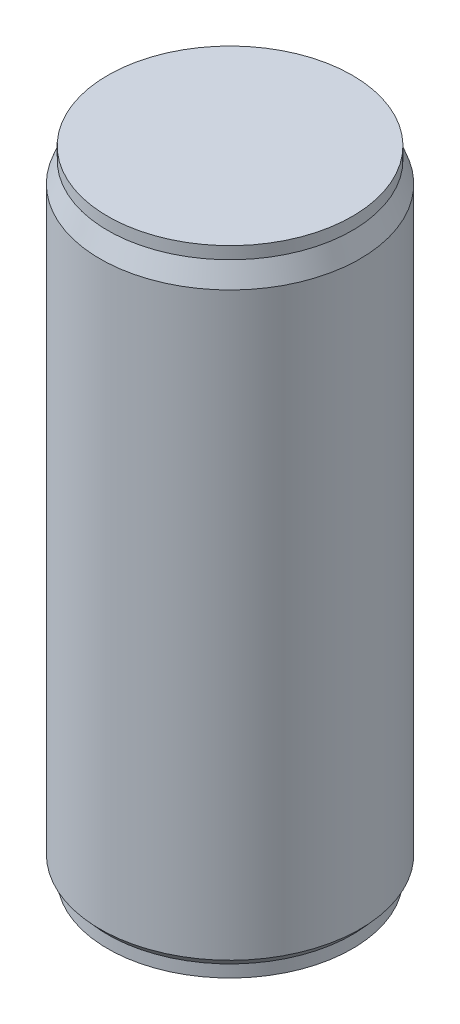
SolidWorks part; units mm, degrees
ref_plane "Front Plane" through (0, 0, 0) normal (0, 0, 1) x (1, 0, 0)
ref_plane "Top Plane" through (0, 0, 0) normal (0, 1, 0) x (1, 0, 0)
ref_plane "Right Plane" through (0, 0, 0) normal (1, 0, 0) x (0, 0, -1)
sketch "Sketch1" plane through (0, 0, 0) normal (0, 0, 1) x (1, 0, 0)
  line L0 (0, 0) -> (0, 131.7625)
  line L1 (0, 131.7625) -> (25.4, 131.7625)
  line L2 (25.4, 131.7625) -> (25.4, 129.2225)
  line L3 (25.4, 129.2225) -> (26.9875, 124.9045)
  line L4 (26.9875, 124.9045) -> (26.9875, 4.318)
  line L5 (26.9875, 4.318) -> (25.4, 2.54)
  line L6 (25.4, 2.54) -> (25.4, 0)
  line L7 (25.4, 0) -> (0, 0)
  dimension "D1" = 26.9875
  dimension "D2" = 131.7625
  dimension "D3" = 25.4
  dimension "D4" = 2.54
  dimension "D5" = 4.318
  dimension "D6" = 6.858
revolve "Revolve1" add sketch "Sketch1" angle 360 about L0
